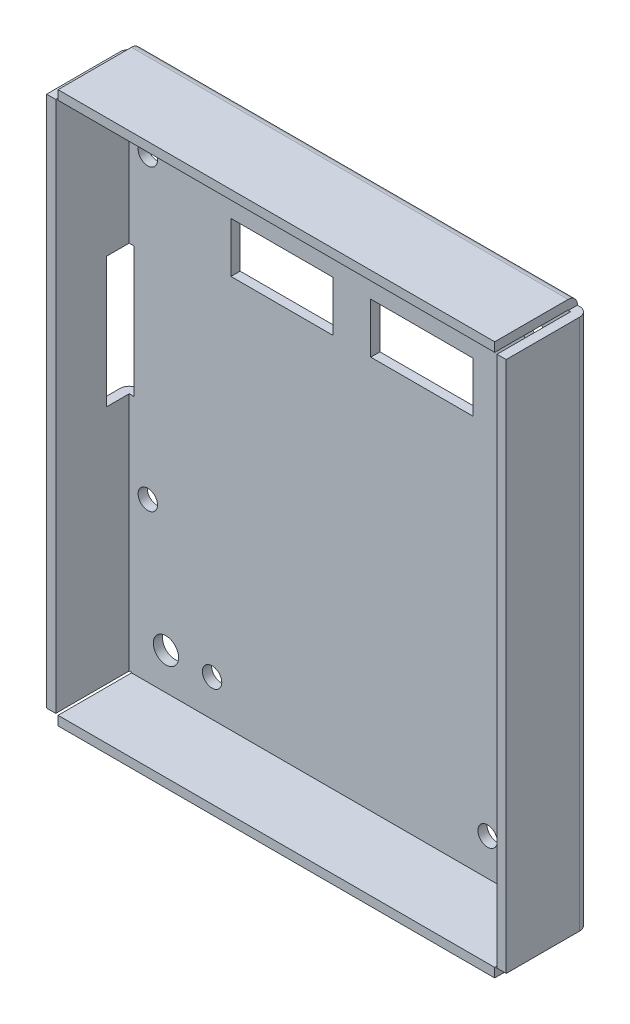
SolidWorks part; units mm, degrees
ref_plane "Front Plane" through (0, 0, 0) normal (0, 0, 1) x (1, 0, 0)
ref_plane "Top Plane" through (0, 0, 0) normal (0, 1, 0) x (1, 0, 0)
ref_plane "Right Plane" through (0, 0, 0) normal (1, 0, 0) x (0, 0, -1)
sketch "Sketch1" plane through (0, 0, 0) normal (0, 0, 1) x (1, 0, 0)
  line L0 (96.6, -86) -> (96.6, -16) construction
  line L1 (0, 0) -> (100.1, 0)
  line L2 (0, 0) -> (0, -120)
  line L3 (0, -120) -> (100.1, -120)
  line L4 (100.1, 0) -> (100.1, -120)
  line L5 (45.4, -31.4) -> (25.15, -31.4) construction
  line L6 (24.15, -21.45) -> (46.4, -21.45)
  line L7 (24.15, -21.45) -> (24.15, -32.4)
  line L8 (24.15, -32.4) -> (46.4, -32.4)
  line L9 (46.4, -21.45) -> (46.4, -32.4)
  line L10 (54.6, -21.45) -> (76.85, -21.45)
  line L11 (54.6, -21.45) -> (54.6, -32.4)
  line L12 (54.6, -32.4) -> (76.85, -32.4)
  line L13 (76.85, -21.45) -> (76.85, -32.4)
  line L14 (25.15, -22.45) -> (45.4, -22.45) construction
  line L15 (25.15, -31.4) -> (25.15, -22.45) construction
  line L16 (45.4, -22.45) -> (45.4, -31.4) construction
  line L17 (55.6, -31.4) -> (55.6, -22.45) construction
  line L18 (20.05, -110) -> (80.05, -110) construction
  line L19 (50.05, -110) -> (50.05, -120) construction
  line L20 (80.05, -110) -> (80.05, -10) construction
  line L21 (80.05, -60) -> (100.1, -60) construction
  circle A0 centre (10, -10) radius 2.75
  circle A1 centre (90.1, -10) radius 2.75
  circle A2 centre (10, -110) radius 2.75
  circle A3 centre (6.05, -18.5) radius 2.11
  circle A4 centre (6.05, -83.5) radius 2.11
  circle A5 centre (94.05, -18.5) radius 2.11
  circle A6 centre (94.05, -83.5) radius 2.11
  circle A7 centre (10, -10) radius 5 construction
  circle A8 centre (10, -110) radius 5 construction
  circle A9 centre (20.05, -10) radius 2.11
  circle A10 centre (80.05, -10) radius 2.11
  circle A11 centre (20.05, -110) radius 2.11
  circle A12 centre (80.05, -110) radius 2.11
  circle A13 centre (90.1, -110) radius 2.75
  circle A14 centre (50.05, -10) radius 2.75
  dimension "D7" = 4.22
  dimension "D8" = 5.5
  dimension "D9" = 10
  dimension "D15" = 4.22
  dimension "D1" = 120
  dimension "D2" = 10
  dimension "D3" = 10
  dimension "D4" = 10
  dimension "D5" = 3.5
  dimension "D6" = 10
  dimension "D10" = 1
  dimension "D11" = 1
  dimension "D12" = 1
  dimension "D13" = 1
  dimension "D14" = 1
  dimension "D16" = 100
  dimension "D17" = 60
extrude "Boss-Extrude1" add sketch "Sketch1" along normal blind 2
sketch "Sketch2" plane through (0, 0, 2) normal (0, 0, 1) x (1, 0, 0)
  line L0 (0, 0) -> (0, -120) construction
  line L1 (0, -2.1) -> (2, -2.1)
  line L2 (0, -2.1) -> (0, -117.9)
  line L3 (0, -117.9) -> (2, -117.9)
  line L4 (2, -2.1) -> (2, -117.9)
  line L7 (100.1, 0) -> (0, 0) construction
  line L11 (0, -120) -> (100.1, -120) construction
  dimension "D2" = 2.1
  dimension "D4" = 2
  dimension "D7" = 2.1
extrude "Boss-Extrude2" add sketch "Sketch2" along normal blind 16
ref_plane "Plane1" through (50.05, 0, 0) normal (1, 0, 0) x (0, 0, -1)
mirror "Mirror1" about plane through (50.05, 0, 0) normal (1, 0, 0) of "Boss-Extrude2"
sketch "Sketch4" plane through (0, 0, 2) normal (0, 0, 1) x (1, 0, 0)
  line L0 (100.1, 0) -> (0, 0) construction
  line L1 (2.5, 0) -> (97.6, 0)
  line L2 (2.5, 0) -> (2.5, -2)
  line L3 (2.5, -2) -> (97.6, -2)
  line L4 (97.6, 0) -> (97.6, -2)
  line L6 (0, -120) -> (100.1, -120) construction
  line L7 (2.5, -118) -> (97.6, -118)
  line L8 (2.5, -118) -> (2.5, -120)
  line L9 (2.5, -120) -> (97.6, -120)
  line L10 (97.6, -118) -> (97.6, -120)
  line L11 (98.1, -117.9) -> (98.1, -2.1) construction
  line L12 (2, -117.9) -> (2, -2.1) construction
  dimension "D1" = 0.5
  dimension "D2" = 2
  dimension "D3" = 0.5
extrude "Boss-Extrude3" add sketch "Sketch4" along normal up to surface (16 mm away) up to face at (1, -60, 18)
sketch "Sketch5" plane through (0, 0, 0) normal (0, 0, -1) x (-1, 0, 0)
  line L0 (-100.1, 0) -> (0, 0) construction
  line L1 (-2.5, 0) -> (0, 0)
  line L2 (-2.5, 0) -> (-2.5, -2.1)
  line L3 (-2.5, -2.1) -> (0, -2.1)
  line L4 (0, 0) -> (0, -2.1)
  line L5 (0, 0) -> (0, -120) construction
  line L6 (-100.1, -120) -> (-100.1, 0) construction
  line L7 (-100.1, -120) -> (-97.6, -120)
  line L8 (-100.1, -120) -> (-100.1, -117.9)
  line L9 (-100.1, -117.9) -> (-97.6, -117.9)
  line L10 (-97.6, -120) -> (-97.6, -117.9)
  line L11 (0, -120) -> (-2.5, -120)
  line L12 (0, -120) -> (0, -117.9)
  line L13 (0, -117.9) -> (-2.5, -117.9)
  line L14 (-2.5, -120) -> (-2.5, -117.9)
  line L15 (-100.1, 0) -> (-97.6, 0)
  line L16 (-100.1, 0) -> (-100.1, -2.1)
  line L17 (-100.1, -2.1) -> (-97.6, -2.1)
  line L18 (-97.6, 0) -> (-97.6, -2.1)
extrude "Cut-Extrude1" cut sketch "Sketch5" against normal blind 2
sketch "Sketch6" plane through (0, 0, 0) normal (-1, 0, 0) x (0, 0, 1)
  line L0 (6, -38.2) -> (6, -64.6) construction
  line L1 (0, -37.2) -> (7, -37.2)
  line L2 (0, -37.2) -> (0, -65.6)
  line L3 (0, -65.6) -> (7, -65.6)
  line L4 (7, -37.2) -> (7, -65.6)
  line L5 (2.5, -38.2) -> (6, -38.2) construction
  line L8 (2.5, -64.6) -> (6, -64.6) construction
  line L9 (0, -2.1) -> (0, -117.9) construction
  dimension "D1" = 1
  dimension "D2" = 1
  dimension "D4" = 1
extrude "Cut-Extrude2" cut sketch "Sketch6" against normal blind 3
fillet "Fillet2" radius 2 5 edges at (50.05, -120, 0) (100.1, -60, 0) (0, -91.75, 0) (0, -19.65, 0) (50.05, 0, 0)
